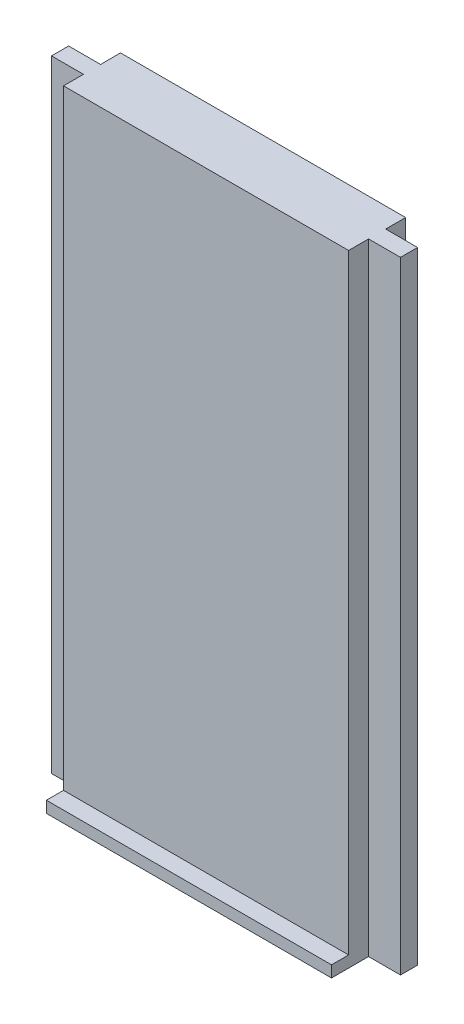
SolidWorks part; units mm, degrees
ref_plane "Front Plane" through (0, 0, 0) normal (0, 0, 1) x (1, 0, 0)
ref_plane "Top Plane" through (0, 0, 0) normal (0, 1, 0) x (1, 0, 0)
ref_plane "Right Plane" through (0, 0, 0) normal (1, 0, 0) x (0, 0, -1)
sketch "Sketch1" plane through (0, 0, 0) normal (0, 1, 0) x (1, 0, 0)
  line L0 (-12.5, 0.75) -> (-12.5, 2.5)
  line L1 (-12.5, -2.5) -> (12.5, -2.5)
  line L2 (-12.5, -2.5) -> (-12.5, -0.75)
  line L3 (-12.5, 2.5) -> (12.5, 2.5)
  line L4 (12.5, -2.5) -> (12.5, -0.75)
  line L5 (-12.5, -2.5) -> (12.5, 2.5) construction
  line L6 (-12.5, 2.5) -> (12.5, -2.5) construction
  line L7 (-12.5, -0.75) -> (-15.3, -0.75)
  line L9 (-12.5, 0.75) -> (-15.3, 0.75)
  line L10 (-15.3, -0.75) -> (-15.3, 0.75)
  line L11 (0, -2.5) -> (0, 2.5) construction
  line L12 (12.5, -0.75) -> (15.3, -0.75)
  line L13 (15.3, -0.75) -> (15.3, 0.75)
  line L14 (12.5, 0.75) -> (15.3, 0.75)
  line L15 (12.5, 0.75) -> (12.5, 2.5)
  point P0 (0, 0)
  point P6 (-12.5, 0)
  dimension "D1" = 25
  dimension "D2" = 5
  dimension "D3" = 1.5
  dimension "D4" = 2.8
  dimension "D5" = 1.75
extrude "Boss-Extrude1" add sketch "Sketch1" along normal blind 54.5
sketch "Sketch2" plane through (0, 0, 0) normal (0, 1, 0) x (1, 0, 0)
  line L6 (-12.5, -2.5) -> (12.5, -2.5)
  line L7 (-12.5, -2.5) -> (-12.5, -4)
  line L8 (-12.5, -4) -> (12.5, -4)
  line L9 (12.5, -2.5) -> (12.5, -4)
  dimension "D1" = 25
  dimension "D2" = 4
extrude "Boss-Extrude2" add sketch "Sketch2" along normal blind 1
